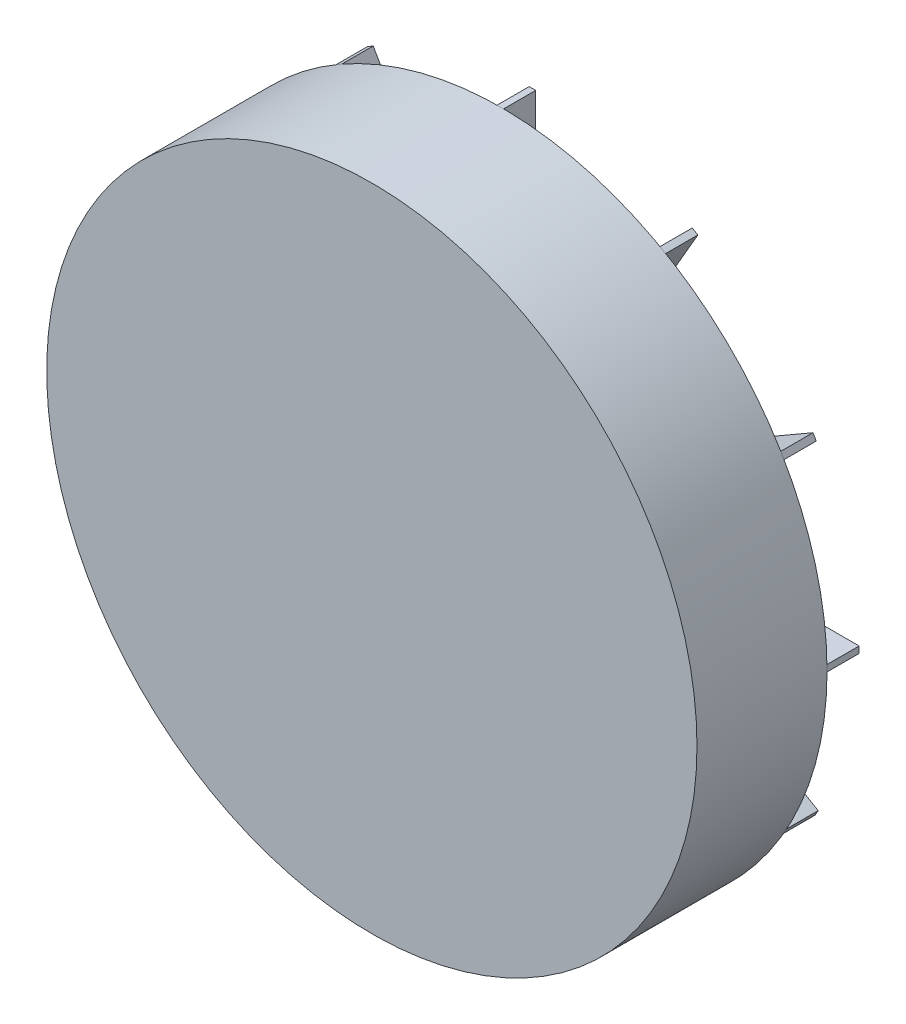
SolidWorks part; units mm, degrees
ref_plane "Front Plane" through (0, 0, 0) normal (0, 0, 1) x (1, 0, 0)
ref_plane "Top Plane" through (0, 0, 0) normal (0, 1, 0) x (1, 0, 0)
ref_plane "Right Plane" through (0, 0, 0) normal (1, 0, 0) x (0, 0, -1)
sketch "Sketch1" plane through (0, 0, 0) normal (0, 0, 1) x (1, 0, 0)
  circle A0 centre (0, 0) radius 100
  dimension "D1" = 200
extrude "Boss-Extrude1" add sketch "Sketch1" along normal blind 40
sketch "Sketch3" plane through (0, 0, 0) normal (0, 0, 1) x (1, 0, 0)
  line L0 (0, 0) -> (-36.2187, -27.3535) construction
  line L1 (-0.6027, 0.798) -> (-36.8213, -26.5555)
  line L2 (0.6027, -0.798) -> (-35.616, -28.1515)
  line L3 (-0.6027, 0.798) -> (0.6027, -0.798)
  line L5 (-35.616, -28.1515) -> (-33.808, -30.5455)
  line L6 (-33.808, -30.5455) -> (-60.9708, -46.0471)
  line L7 (-36.8213, -26.5555) -> (-38.6294, -24.1615)
  line L8 (-38.6294, -24.1615) -> (-60.9708, -46.0471)
  line L9 (-0.6027, 99.9982) -> (-0.6027, 82.4227) construction
  line L16 (-1.6027, 99.861) -> (-1.6027, 82.4227)
  line L20 (0.3973, 99.861) -> (0.3973, 82.4227)
  line L24 (-1.6027, 99.9982) -> (-1.6027, 82.4227) construction
  line L28 (0.3973, 99.9982) -> (0.3973, 82.4227) construction
  line L32 (0.3973, 99.861) -> (-1.6027, 99.861)
  line L36 (48.5426, 87.2835) -> (39.8234, 72.1815)
  line L40 (50.2746, 86.2835) -> (41.5555, 71.1815)
  line L44 (50.2746, 86.2835) -> (48.5426, 87.2835)
  line L48 (49.4772, 86.9023) -> (40.6894, 71.6815) construction
  line L52 (85.6809, 51.3185) -> (70.5788, 42.5993)
  line L56 (86.6809, 49.5864) -> (71.5788, 40.8673)
  line L57 (86.6809, 49.5864) -> (85.6809, 51.3185)
  line L58 (-36.2187, -27.3535) -> (-60.9708, -46.0471) construction
  line L59 (86.2996, 50.521) -> (71.0788, 41.7333) construction
  line L60 (99.861, 1.6027) -> (82.4227, 1.6027)
  line L61 (99.861, -0.3973) -> (82.4227, -0.3973)
  line L62 (99.861, -0.3973) -> (99.861, 1.6027)
  line L63 (99.9982, 0.6027) -> (82.4227, 0.6027) construction
  line L64 (87.2835, -48.5426) -> (72.1815, -39.8234)
  line L65 (86.2835, -50.2746) -> (71.1815, -41.5555)
  line L66 (86.2835, -50.2746) -> (87.2835, -48.5426)
  line L67 (86.9023, -49.4772) -> (71.6815, -40.6894) construction
  line L68 (51.3185, -85.6809) -> (42.5993, -70.5788)
  line L69 (49.5864, -86.6809) -> (40.8673, -71.5788)
  line L70 (49.5864, -86.6809) -> (51.3185, -85.6809)
  line L71 (50.521, -86.2996) -> (41.7333, -71.0788) construction
  line L72 (1.6027, -99.861) -> (1.6027, -82.4227)
  line L73 (-0.3973, -99.861) -> (-0.3973, -82.4227)
  line L74 (-0.3973, -99.861) -> (1.6027, -99.861)
  line L75 (0.6027, -99.9982) -> (0.6027, -82.4227) construction
  line L76 (-48.5426, -87.2835) -> (-39.8234, -72.1815)
  line L77 (-50.2746, -86.2835) -> (-41.5555, -71.1815)
  line L78 (-50.2746, -86.2835) -> (-48.5426, -87.2835)
  line L79 (-49.4772, -86.9023) -> (-40.6894, -71.6815) construction
  line L80 (-85.6809, -51.3185) -> (-70.5788, -42.5993)
  line L81 (-86.6809, -49.5864) -> (-71.5788, -40.8673)
  line L82 (-86.6809, -49.5864) -> (-85.6809, -51.3185)
  line L83 (-86.2996, -50.521) -> (-71.0788, -41.7333) construction
  line L84 (-99.861, -1.6027) -> (-82.4227, -1.6027)
  line L85 (-99.861, 0.3973) -> (-82.4227, 0.3973)
  line L86 (-99.861, 0.3973) -> (-99.861, -1.6027)
  line L87 (-99.9982, -0.6027) -> (-82.4227, -0.6027) construction
  line L88 (-87.2835, 48.5426) -> (-72.1815, 39.8234)
  line L89 (-86.2835, 50.2746) -> (-71.1815, 41.5555)
  line L90 (-86.2835, 50.2746) -> (-87.2835, 48.5426)
  line L91 (-86.9023, 49.4772) -> (-71.6815, 40.6894) construction
  line L92 (-51.3185, 85.6809) -> (-42.5993, 70.5788)
  line L93 (-49.5864, 86.6809) -> (-40.8673, 71.5788)
  line L94 (-49.5864, 86.6809) -> (-51.3185, 85.6809)
  line L95 (-50.521, 86.2996) -> (-41.7333, 71.0788) construction
  circle A0 centre (0, 0) radius 100 construction
  arc A13 (41.5555, 71.1815) -> (39.8234, 72.1815) centre (40.6894, 71.6815) cw
  arc A14 (71.5788, 40.8673) -> (70.5788, 42.5993) centre (71.0788, 41.7333) cw
  arc A15 (82.4227, -0.3973) -> (82.4227, 1.6027) centre (82.4227, 0.6027) cw
  arc A16 (71.1815, -41.5555) -> (72.1815, -39.8234) centre (71.6815, -40.6894) cw
  arc A17 (40.8673, -71.5788) -> (42.5993, -70.5788) centre (41.7333, -71.0788) cw
  arc A18 (-0.3973, -82.4227) -> (1.6027, -82.4227) centre (0.6027, -82.4227) cw
  arc A19 (-41.5555, -71.1815) -> (-39.8234, -72.1815) centre (-40.6894, -71.6815) cw
  arc A20 (-71.5788, -40.8673) -> (-70.5788, -42.5993) centre (-71.0788, -41.7333) cw
  arc A21 (-82.4227, 0.3973) -> (-82.4227, -1.6027) centre (-82.4227, -0.6027) cw
  arc A22 (-71.1815, 41.5555) -> (-72.1815, 39.8234) centre (-71.6815, 40.6894) cw
  arc A23 (0.3973, 82.4227) -> (-1.6027, 82.4227) centre (-0.6027, 82.4227) cw
  arc A24 (-40.8673, 71.5788) -> (-42.5993, 70.5788) centre (-41.7333, 71.0788) cw
  dimension "D3" = 4
  dimension "D4" = 4
  dimension "D1" = 1
  dimension "D2" = 1
  dimension "D5" = 1
  dimension "D6" = 1
  dimension "D7" = 12
extrude "Boss-Extrude4" add sketch "Sketch3" against normal blind 10
